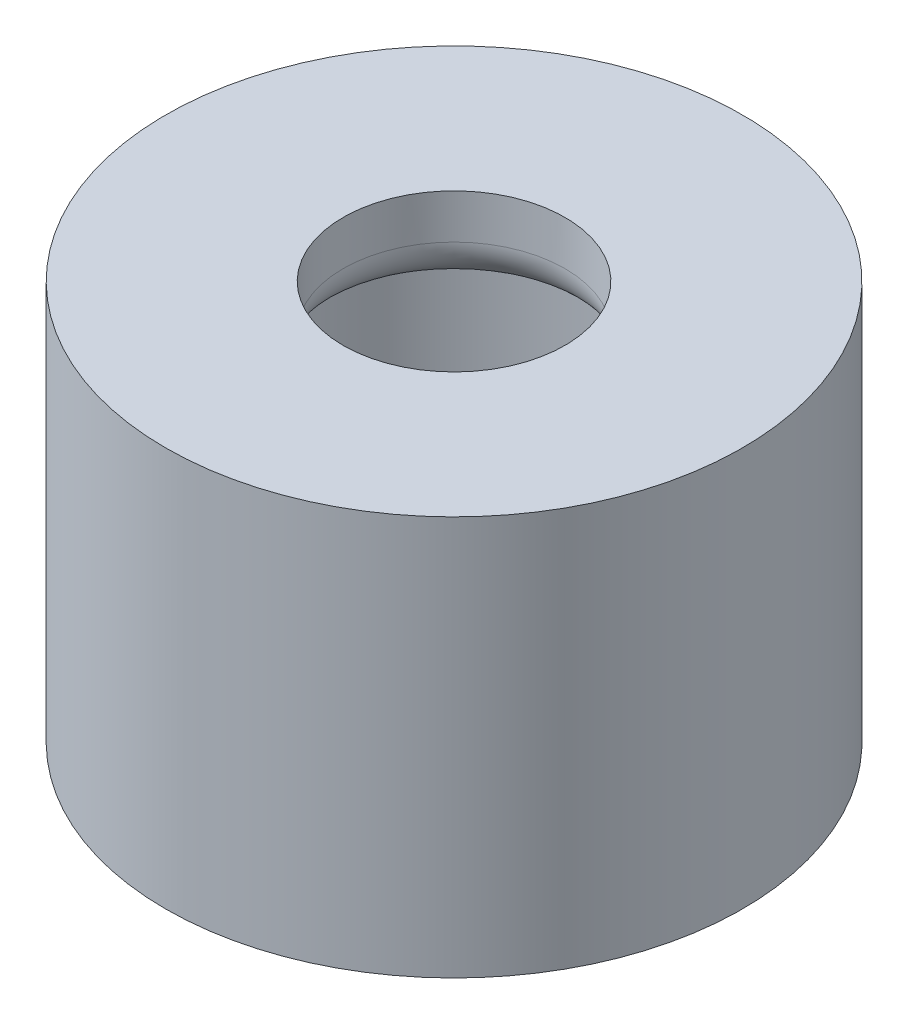
SolidWorks part; units mm, degrees
ref_plane "Front Plane" through (0, 0, 0) normal (0, 0, 1) x (1, 0, 0)
ref_plane "Top Plane" through (0, 0, 0) normal (0, 1, 0) x (1, 0, 0)
ref_plane "Right Plane" through (0, 0, 0) normal (1, 0, 0) x (0, 0, -1)
sketch "Sketch1" plane through (0, 0, 0) normal (0, 1, 0) x (1, 0, 0)
  circle A0 centre (0, 0) radius 6.5
  dimension "D1" = 13
extrude "Boss-Extrude1" add sketch "Sketch1" along normal blind 9
sketch "Sketch2" plane through (0, 9, 0) normal (0, 1, 0) x (1, 0, 0)
  circle A0 centre (0, 0) radius 2.5
  dimension "D1" = 5
sketch "Sketch3" plane through (0, 0, 0) normal (0, -1, 0) x (1, 0, 0)
  circle A0 centre (0, 0) radius 4.5
  dimension "D1" = 9
extrude "Cut-Extrude1" cut sketch "Sketch3" against normal blind 7
extrude "Cut-Extrude2" cut sketch "Sketch2" against normal blind 3 contours A0
fillet "Fillet2" radius 1 1 edges at (0, 7, -2.5)
